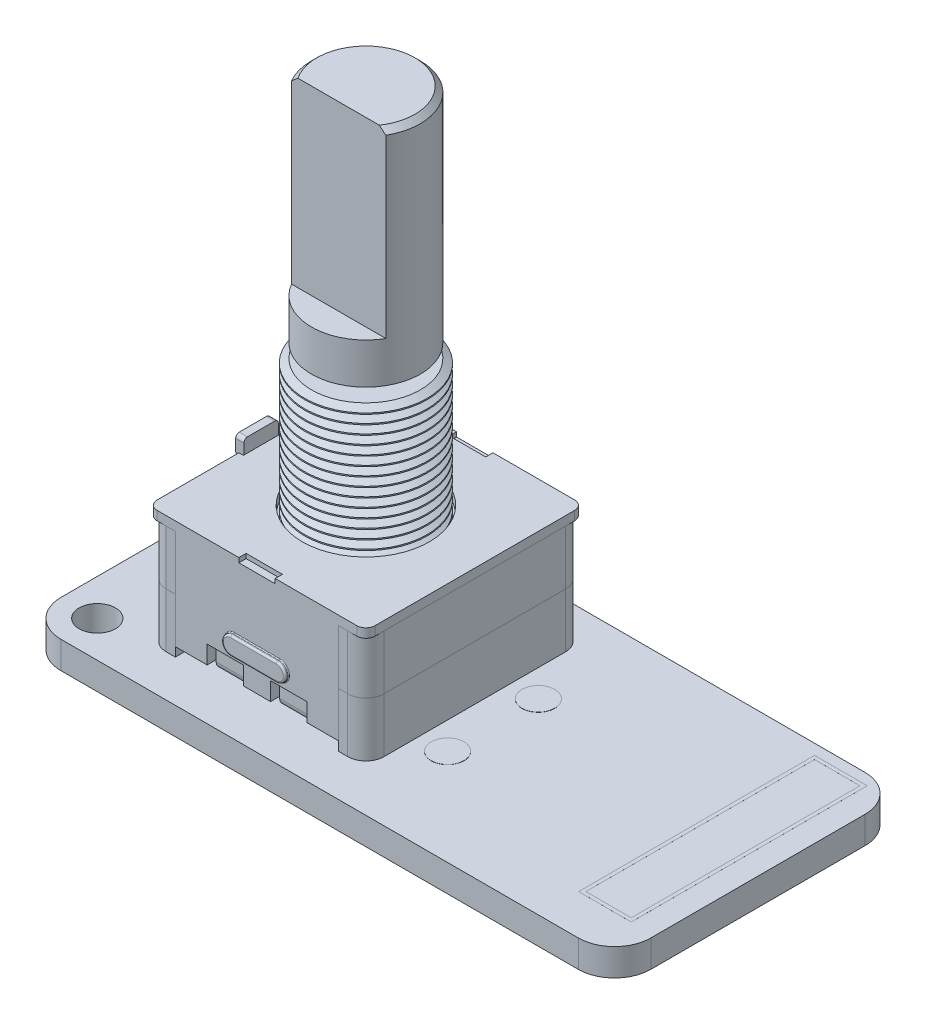
SolidWorks part; units mm, degrees
other "Knob Stem"
material "6061-T6 (SS)"
ref_plane "Front Plane" through (0, 0, 0) normal (0, 0, 1) x (1, 0, 0)
ref_plane "Top Plane" through (0, 0, 0) normal (0, 1, 0) x (1, 0, 0)
ref_plane "Right Plane" through (0, 0, 0) normal (1, 0, 0) x (0, 0, -1)
sketch "Sketch1" plane through (0, 0, 0) normal (0, 1, 0) x (1, 0, 0)
  line L1 (-11, 8) -> (21.5, 8)
  line L2 (-11, 8) -> (-11, -7.8)
  line L3 (-11, -7.8) -> (21.5, -7.8)
  line L4 (21.5, 8) -> (21.5, -7.8)
  dimension "D1" = 32.5
  dimension "D2" = 15.8
  dimension "D3" = 8
  dimension "D4" = 11
extrude "Boss-Extrude1" add sketch "Sketch1" against normal blind 1.5
sketch "Sketch3" plane through (0, -1.5, 0) normal (0, -1, 0) x (1, 0, 0)
  line L0 (-3.75, -1) -> (3.75, -1) construction
  line L1 (-0.5, 0.625) -> (0.5, 0.625)
  line L2 (-0.5, 0.625) -> (-0.5, -2.625)
  line L3 (-0.5, -2.625) -> (0.5, -2.625)
  line L4 (0.5, 0.625) -> (0.5, -2.625)
  line L5 (-0.5, 0.625) -> (0.5, -2.625) construction
  line L6 (-0.5, -2.625) -> (0.5, 0.625) construction
  line L7 (0, -1) -> (0, 0) construction
  line L8 (3.25, 0.625) -> (4.25, 0.625)
  line L9 (3.25, 0.625) -> (3.25, -2.625)
  line L10 (3.25, -2.625) -> (4.25, -2.625)
  line L11 (4.25, 0.625) -> (4.25, -2.625)
  line L12 (3.25, 0.625) -> (4.25, -2.625) construction
  line L13 (3.25, -2.625) -> (4.25, 0.625) construction
  line L14 (-3.25, 0.625) -> (-4.25, 0.625)
  line L15 (-3.25, 0.625) -> (-3.25, -2.625)
  line L16 (-3.25, -2.625) -> (-4.25, -2.625)
  line L17 (-4.25, 0.625) -> (-4.25, -2.625)
  line L18 (-3.25, 0.625) -> (-4.25, -2.625) construction
  line L19 (-3.25, -2.625) -> (-4.25, 0.625) construction
  line L20 (21.5, -8) -> (-11, -8) construction
  point P0 (0, -1)
  dimension "D1" = 3.25
  dimension "D2" = 1
  dimension "D3" = 8.5
  dimension "D4" = 7
extrude "Boss-Extrude2" add sketch "Sketch3" along normal blind 0.001
sketch "Sketch4" plane through (0, -1.501, 0) normal (0, -1, 0) x (1, 0, 0)
  line L0 (-0.5, -1) -> (0.5, -1) construction
  line L2 (3.25, -1) -> (4.25, -1) construction
  line L3 (3.25, 0.625) -> (3.25, -2.625) construction
  line L4 (4.25, -2.625) -> (4.25, 0.625) construction
  line L5 (-3.25, -1) -> (-4.25, -1) construction
  line L6 (-3.25, -2.625) -> (-3.25, 0.625) construction
  line L7 (-4.25, 0.625) -> (-4.25, -2.625) construction
  line L9 (-0.625, 0.125) -> (0.625, 0.125)
  line L10 (-0.625, 0.125) -> (-0.625, -2.125)
  line L11 (-0.625, -2.125) -> (0.625, -2.125)
  line L12 (0.625, 0.125) -> (0.625, -2.125)
  line L13 (-0.625, 0.125) -> (0.625, -2.125) construction
  line L14 (-0.625, -2.125) -> (0.625, 0.125) construction
  line L15 (3.125, 0.125) -> (4.375, 0.125)
  line L16 (3.125, 0.125) -> (3.125, -2.125)
  line L17 (3.125, -2.125) -> (4.375, -2.125)
  line L18 (4.375, 0.125) -> (4.375, -2.125)
  line L19 (3.125, 0.125) -> (4.375, -2.125) construction
  line L20 (3.125, -2.125) -> (4.375, 0.125) construction
  line L21 (-4.375, 0.125) -> (-3.125, 0.125)
  line L22 (-4.375, 0.125) -> (-4.375, -2.125)
  line L23 (-4.375, -2.125) -> (-3.125, -2.125)
  line L24 (-3.125, 0.125) -> (-3.125, -2.125)
  line L25 (-4.375, 0.125) -> (-3.125, -2.125) construction
  line L26 (-4.375, -2.125) -> (-3.125, 0.125) construction
  line L27 (-0.5, 0.625) -> (-0.5, -2.625) construction
  line L28 (0.5, -2.625) -> (0.5, 0.625) construction
  point P17 (0, -1)
  point P22 (3.75, -1)
  point P27 (-3.75, -1)
  dimension "D1" = 1.25
  dimension "D2" = 2.25
extrude "Boss-Extrude3" add sketch "Sketch4" along normal blind 0.3
sketch "Sketch5" plane through (0, -1.801, 0) normal (0, -1, 0) x (1, 0, 0)
  line L0 (-0.625, 0.125) -> (-0.625, -2.125) construction
  line L2 (-0.625, -1) -> (-3.125, -1) construction
  line L3 (-3.125, -1) -> (-4.375, -1) construction
  line L4 (-4.375, 0.125) -> (-4.375, -2.125) construction
  line L5 (-3.125, -2.125) -> (-3.125, 0.125) construction
  line L6 (0.625, -1) -> (3.125, -1) construction
  line L7 (3.125, 0.125) -> (3.125, -2.125) construction
  line L8 (3.125, -1) -> (4.375, -1) construction
  line L9 (4.375, -2.125) -> (4.375, 0.125) construction
  line L10 (0.625, -2.125) -> (0.625, 0.125) construction
  line L15 (-0.625, -1) -> (0.625, -1) construction
  line L17 (-0.625, -0.1) -> (0.625, -0.1)
  line L18 (-4.375, -0.1) -> (-3.125, -0.1)
  line L19 (-4.375, -0.1) -> (-4.375, -1.9)
  line L20 (-4.375, -1.9) -> (-3.125, -1.9)
  line L21 (-3.125, -0.1) -> (-3.125, -1.9)
  line L22 (-4.375, -0.1) -> (-3.125, -1.9) construction
  line L23 (-4.375, -1.9) -> (-3.125, -0.1) construction
  line L24 (3.125, -0.1) -> (4.375, -0.1)
  line L25 (3.125, -0.1) -> (3.125, -1.9)
  line L26 (3.125, -1.9) -> (4.375, -1.9)
  line L27 (4.375, -0.1) -> (4.375, -1.9)
  line L28 (3.125, -0.1) -> (4.375, -1.9) construction
  line L29 (3.125, -1.9) -> (4.375, -0.1) construction
  line L30 (-0.625, -0.1) -> (-0.625, -1.9)
  line L31 (-0.625, -1.9) -> (0.625, -1.9)
  line L32 (0.625, -0.1) -> (0.625, -1.9)
  line L33 (-0.625, -0.1) -> (0.625, -1.9) construction
  line L34 (-0.625, -1.9) -> (0.625, -0.1) construction
  point P4 (0, -1)
  point P24 (-3.75, -1)
  point P29 (3.75, -1)
  dimension "D1" = 1.8
extrude "Boss-Extrude4" add sketch "Sketch5" along normal blind 0.1
sketch "Sketch6" plane through (0, -1.5, 0) normal (0, -1, 0) x (1, 0, 0)
  line L0 (18.75, -8) -> (18.75, -6) construction
  line L1 (-7, 2.5) -> (7, 2.5) construction
  line L2 (-7, 2.5) -> (-7, -2.5) construction
  line L3 (-7, -2.5) -> (7, -2.5) construction
  line L4 (7, 2.5) -> (7, -2.5) construction
  line L5 (-7, 2.5) -> (7, -2.5) construction
  line L6 (-7, -2.5) -> (7, 2.5) construction
  line L7 (21.5, -8) -> (-11, -8) construction
  line L8 (18.75, -6) -> (18.75, -3.46) construction
  line L9 (18.75, -3.46) -> (18.75, -0.92) construction
  line L10 (18.75, -0.92) -> (18.75, 1.62) construction
  line L11 (18.75, 1.62) -> (18.75, 4.16) construction
  line L12 (21.5, 7.8) -> (21.5, -8) construction
  circle A0 centre (7, 2.5) radius 0.6
  circle A1 centre (7, -2.5) radius 0.6
  circle A2 centre (-7, -2.5) radius 0.6
  circle A3 centre (-7, 2.5) radius 0.6
  circle A4 centre (-7, 0) radius 0.6
  circle A5 centre (18.75, 4.16) radius 0.6
  circle A6 centre (18.75, 1.62) radius 0.6
  circle A7 centre (18.75, -0.92) radius 0.6
  circle A8 centre (18.75, -3.46) radius 0.6
  circle A9 centre (18.75, -6) radius 0.6
  point P0 (0, 0)
  dimension "D3" = 1.2
  dimension "D4" = 2.54
  dimension "D1" = 5
  dimension "D2" = 14
  dimension "D5" = 2
  dimension "D6" = 2.75
extrude "Boss-Extrude5" add sketch "Sketch6" along normal blind 0.01
sketch "Sketch7" plane through (0, -1.5, 0) normal (0, -1, 0) x (1, 0, 0)
  line L1 (-7.325, -2.175) -> (-6.675, -2.175)
  line L2 (-7.325, -2.175) -> (-7.325, -2.825)
  line L3 (-7.325, -2.825) -> (-6.675, -2.825)
  line L4 (-6.675, -2.175) -> (-6.675, -2.825)
  line L5 (-7.325, -2.175) -> (-6.675, -2.825) construction
  line L6 (-7.325, -2.825) -> (-6.675, -2.175) construction
  line L7 (-7.325, 0.325) -> (-6.675, 0.325)
  line L8 (-7.325, 0.325) -> (-7.325, -0.325)
  line L9 (-7.325, -0.325) -> (-6.675, -0.325)
  line L10 (-6.675, 0.325) -> (-6.675, -0.325)
  line L11 (-7.325, 0.325) -> (-6.675, -0.325) construction
  line L12 (-7.325, -0.325) -> (-6.675, 0.325) construction
  line L13 (-7.325, 2.825) -> (-6.675, 2.825)
  line L14 (-7.325, 2.825) -> (-7.325, 2.175)
  line L15 (-7.325, 2.175) -> (-6.675, 2.175)
  line L16 (-6.675, 2.825) -> (-6.675, 2.175)
  line L17 (-7.325, 2.825) -> (-6.675, 2.175) construction
  line L18 (-7.325, 2.175) -> (-6.675, 2.825) construction
  line L19 (6.675, -2.175) -> (7.325, -2.175)
  line L20 (6.675, -2.175) -> (6.675, -2.825)
  line L21 (6.675, -2.825) -> (7.325, -2.825)
  line L22 (7.325, -2.175) -> (7.325, -2.825)
  line L23 (6.675, -2.175) -> (7.325, -2.825) construction
  line L24 (6.675, -2.825) -> (7.325, -2.175) construction
  line L25 (6.675, 2.825) -> (7.325, 2.825)
  line L26 (6.675, 2.825) -> (6.675, 2.175)
  line L27 (6.675, 2.175) -> (7.325, 2.175)
  line L28 (7.325, 2.825) -> (7.325, 2.175)
  line L29 (6.675, 2.825) -> (7.325, 2.175) construction
  line L30 (6.675, 2.175) -> (7.325, 2.825) construction
  line L31 (18.425, 4.485) -> (19.075, 4.485)
  line L32 (18.425, 4.485) -> (18.425, 3.835)
  line L33 (18.425, 3.835) -> (19.075, 3.835)
  line L34 (19.075, 4.485) -> (19.075, 3.835)
  line L35 (18.425, 4.485) -> (19.075, 3.835) construction
  line L36 (18.425, 3.835) -> (19.075, 4.485) construction
  line L37 (18.425, 1.945) -> (19.075, 1.945)
  line L38 (18.425, 1.945) -> (18.425, 1.295)
  line L39 (18.425, 1.295) -> (19.075, 1.295)
  line L40 (19.075, 1.945) -> (19.075, 1.295)
  line L41 (18.425, 1.945) -> (19.075, 1.295) construction
  line L42 (18.425, 1.295) -> (19.075, 1.945) construction
  line L43 (18.425, -0.595) -> (19.075, -0.595)
  line L44 (18.425, -0.595) -> (18.425, -1.245)
  line L45 (18.425, -1.245) -> (19.075, -1.245)
  line L46 (19.075, -0.595) -> (19.075, -1.245)
  line L47 (18.425, -0.595) -> (19.075, -1.245) construction
  line L48 (18.425, -1.245) -> (19.075, -0.595) construction
  line L49 (18.425, -3.135) -> (19.075, -3.135)
  line L50 (18.425, -3.135) -> (18.425, -3.785)
  line L51 (18.425, -3.785) -> (19.075, -3.785)
  line L52 (19.075, -3.135) -> (19.075, -3.785)
  line L53 (18.425, -3.135) -> (19.075, -3.785) construction
  line L54 (18.425, -3.785) -> (19.075, -3.135) construction
  line L55 (18.425, -5.675) -> (19.075, -5.675)
  line L56 (18.425, -5.675) -> (18.425, -6.325)
  line L57 (18.425, -6.325) -> (19.075, -6.325)
  line L58 (19.075, -5.675) -> (19.075, -6.325)
  line L59 (18.425, -5.675) -> (19.075, -6.325) construction
  line L60 (18.425, -6.325) -> (19.075, -5.675) construction
  point P0 (-7, -2.5)
  point P5 (-7, 0)
  point P11 (-7, 2.5)
  point P17 (7, -2.5)
  point P23 (7, 2.5)
  point P29 (18.75, 4.16)
  point P35 (18.75, 1.62)
  point P41 (18.75, -0.92)
  point P47 (18.75, -3.46)
  point P53 (18.75, -6)
  dimension "D1" = 0.65
sketch "Sketch9" plane through (0, -1.5, 0) normal (0, -1, 0) x (1, 0, 0)
  line L0 (3.25, 0.625) -> (4.25, -2.625) construction
  line L1 (-0.8, 0.75) -> (0.8, 0.75)
  line L2 (-0.8, 0.75) -> (-0.8, -0.875)
  line L3 (-0.8, -2.75) -> (0.8, -2.75)
  line L4 (0.8, 0.75) -> (0.8, -0.875)
  line L5 (-0.8, 0.75) -> (0.8, -2.75) construction
  line L6 (-0.8, -2.75) -> (0.8, 0.75) construction
  line L7 (2.95, 0.75) -> (4.55, 0.75)
  line L8 (2.95, 0.75) -> (2.95, -0.875)
  line L9 (2.95, -2.75) -> (4.55, -2.75)
  line L10 (4.55, 0.75) -> (4.55, -0.875)
  line L11 (2.95, 0.75) -> (4.55, -2.75) construction
  line L12 (2.95, -2.75) -> (4.55, 0.75) construction
  line L13 (-4.75, -2.95) -> (-2.75, -2.95)
  line L14 (-4.55, 0.75) -> (-2.95, 0.75)
  line L15 (-4.55, 0.75) -> (-4.55, -0.875)
  line L16 (-4.55, -2.75) -> (-2.95, -2.75)
  line L17 (-2.95, 0.75) -> (-2.95, -0.875)
  line L18 (-4.55, 0.75) -> (-2.95, -2.75) construction
  line L19 (-4.55, -2.75) -> (-2.95, 0.75) construction
  line L20 (-2.75, 0.95) -> (-2.75, -0.875)
  line L21 (-4.75, 0.95) -> (-2.75, 0.95)
  line L22 (-4.75, 0.95) -> (-4.75, -0.875)
  line L23 (-1, 0.95) -> (-1, -0.875)
  line L24 (-1, -2.95) -> (1, -2.95)
  line L25 (1, 0.95) -> (1, -0.875)
  line L26 (-1, 0.95) -> (1, 0.95)
  line L27 (2.75, -2.95) -> (4.75, -2.95)
  line L28 (4.75, 0.95) -> (4.75, -0.875)
  line L29 (2.75, 0.95) -> (4.75, 0.95)
  line L30 (2.75, 0.95) -> (2.75, -0.875)
  line L31 (0, -0.875) -> (0, -1.125) construction
  line L32 (0, -0.875) -> (-0.8, -0.875) construction
  line L33 (0, -1.125) -> (-0.8, -1.125) construction
  line L34 (0, -0.875) -> (0.8, -0.875) construction
  line L35 (0, -1.125) -> (0.8, -1.125) construction
  line L36 (-0.8, -0.875) -> (-1, -0.875)
  line L37 (-0.8, -1.125) -> (-1, -1.125)
  line L38 (0.8, -0.875) -> (1, -0.875)
  line L39 (0.8, -1.125) -> (1, -1.125)
  line L40 (-0.8, -1.125) -> (-0.8, -2.75)
  line L41 (-0.8, 0.75) -> (-0.8, -2.75) construction
  line L42 (-1, -1.125) -> (-1, -2.95)
  line L43 (-1, 0.95) -> (-1, -2.95) construction
  line L44 (1, -1.125) -> (1, -2.95)
  line L45 (1, 0.95) -> (1, -2.95) construction
  line L46 (0.8, -1.125) -> (0.8, -2.75)
  line L47 (0.8, 0.75) -> (0.8, -2.75) construction
  line L48 (-2.95, 0.75) -> (-0.8, 0.75) construction
  line L49 (1, -0.875) -> (2.75, -0.875) construction
  line L50 (1, -1.125) -> (2.75, -1.125) construction
  line L51 (-1, -0.875) -> (-2.75, -0.875) construction
  line L52 (-1, -1.125) -> (-2.75, -1.125) construction
  line L53 (-2.75, -0.875) -> (-2.95, -0.875)
  line L54 (-2.75, -1.125) -> (-2.95, -1.125)
  line L55 (2.75, -0.875) -> (2.95, -0.875)
  line L56 (2.75, -1.125) -> (2.95, -1.125)
  line L57 (2.95, -0.875) -> (4.55, -0.875) construction
  line L58 (2.95, -1.125) -> (4.55, -1.125) construction
  line L59 (4.55, -0.875) -> (4.75, -0.875)
  line L60 (4.55, -1.125) -> (4.75, -1.125)
  line L61 (2.95, -1.125) -> (2.95, -2.75)
  line L62 (2.95, 0.75) -> (2.95, -2.75) construction
  line L63 (2.75, -1.125) -> (2.75, -2.95)
  line L64 (2.75, 0.95) -> (2.75, -2.95) construction
  line L65 (4.75, -1.125) -> (4.75, -2.95)
  line L66 (4.75, 0.95) -> (4.75, -2.95) construction
  line L67 (4.55, -1.125) -> (4.55, -2.75)
  line L68 (4.55, 0.75) -> (4.55, -2.75) construction
  line L69 (0.8, 0.75) -> (2.95, 0.75) construction
  line L70 (-2.95, -0.875) -> (-4.55, -0.875) construction
  line L71 (-2.95, -1.125) -> (-4.55, -1.125) construction
  line L72 (-4.55, -0.875) -> (-4.75, -0.875)
  line L73 (-4.55, -1.125) -> (-4.75, -1.125)
  line L74 (-4.55, -1.125) -> (-4.55, -2.75)
  line L75 (-4.55, 0.75) -> (-4.55, -2.75) construction
  line L76 (-4.75, -1.125) -> (-4.75, -2.95)
  line L77 (-4.75, 0.95) -> (-4.75, -2.95) construction
  line L78 (-2.75, -1.125) -> (-2.75, -2.95)
  line L79 (-2.75, 0.95) -> (-2.75, -2.95) construction
  line L80 (-2.95, -1.125) -> (-2.95, -2.75)
  line L81 (-2.95, 0.75) -> (-2.95, -2.75) construction
  point P0 (0, -1)
  point P5 (3.75, -1)
  point P13 (-3.75, -1)
  dimension "D1" = 3.5
  dimension "D2" = 1.6
  dimension "D6" = 0.25
  dimension "D3" = 0.2
  dimension "D4" = 0.2
  dimension "D5" = 0.2
extrude "Boss-Extrude7" add sketch "Sketch9" along normal blind 0.001
sketch "Sketch10" plane through (0, -1.5, 0) normal (0, -1, 0) x (1, 0, 0)
  line L0 (-3.75, -2.95) -> (-3.75, -3.25) construction
  line L1 (-4.75, -2.95) -> (-2.75, -2.95) construction
  line L2 (0, -2.95) -> (0, -3.25) construction
  line L3 (-1, -2.95) -> (1, -2.95) construction
  line L4 (3.75, -2.95) -> (3.75, -3.25) construction
  line L5 (2.75, -2.95) -> (4.75, -2.95) construction
  line L6 (-1.25, -3.25) -> (1.25, -3.25) construction
  line L7 (-5, -3.25) -> (-2.5, -3.25) construction
  line L8 (2.5, -3.25) -> (5, -3.25) construction
  line L9 (21.5, -8) -> (-11, -8) construction
  text T0 "R1" font "Calibri" height 0.75
  text T1 "R2" font "Calibri" height 0.75
  text T2 "R3" font "Calibri" height 0.75
  dimension "D1" = 2.5
  dimension "D2" = 4.75
extrude "Boss-Extrude8" add sketch "Sketch10" along normal blind 0.001
sketch "Sketch12" plane through (0, 0, 0) normal (0, 1, 0) x (1, 0, 0)
  line L0 (17.3, 7.42) -> (20.2, 7.42)
  line L1 (17.5, -5.38) -> (20, -5.38)
  line L2 (17.5, -5.38) -> (17.5, 7.22)
  line L3 (17.5, 7.22) -> (20, 7.22)
  line L4 (20, -5.38) -> (20, 7.22)
  line L5 (17.5, -5.38) -> (20, 7.22) construction
  line L6 (17.5, 7.22) -> (20, -5.38) construction
  line L7 (20.2, -5.58) -> (20.2, 7.42)
  line L8 (17.3, -5.58) -> (20.2, -5.58)
  line L9 (17.3, -5.58) -> (17.3, 7.42)
  point P0 (18.75, 0.92)
  dimension "D1" = 12.6
  dimension "D2" = 2.5
  dimension "D3" = 0.2
extrude "Boss-Extrude10" add sketch "Sketch12" along normal blind 0.001
sketch "Sketch13" plane through (0, 0, 0) normal (0, 1, 0) x (1, 0, 0)
  circle A0 centre (-7, -2.5) radius 0.6 construction
  circle A1 centre (-7, -2.5) radius 0.6 construction
  circle A2 centre (-7, 0) radius 0.6 construction
  circle A3 centre (-7, 0) radius 0.6 construction
  circle A4 centre (-7, 2.5) radius 0.6 construction
  circle A5 centre (-7, 2.5) radius 0.6 construction
  circle A6 centre (7, -2.5) radius 0.6 construction
  circle A7 centre (7, -2.5) radius 0.6 construction
  circle A8 centre (7, 2.5) radius 0.6 construction
  circle A9 centre (7, 2.5) radius 0.6 construction
  circle A10 centre (-7, -2.5) radius 0.9
  circle A11 centre (-7, 0) radius 0.9
  circle A12 centre (-7, 2.5) radius 0.9
  circle A13 centre (7, 2.5) radius 0.9
  circle A14 centre (7, -2.5) radius 0.9
  dimension "D1" = 1.8
extrude "Boss-Extrude11" add sketch "Sketch13" along normal blind 0.01
ref_plane "Plane3" through (0, 6.5, 0) normal (0, 1, 0) x (1, 0, 0)
sketch "Sketch27" plane through (0, 6.5, 0) normal (0, 1, 0) x (1, 0, 0)
  line L0 (-6, 0) -> (6, 0) construction
  line L5 (-6, 5) -> (-6, -5)
  line L6 (6, 5) -> (6, -5)
  line L7 (0, 5.5) -> (0, -5.5) construction
  line L8 (-4.5, 5.5) -> (4.5, 5.5)
  line L9 (-4.5, -5.5) -> (4.5, -5.5)
  line L10 (-4.5, 5.5) -> (-4.5, 6)
  line L11 (-4.5, 6) -> (-5, 6)
  line L12 (4.5, 5.5) -> (4.5, 6)
  line L13 (4.5, 6) -> (5, 6)
  line L14 (-4.5, -5.5) -> (-4.5, -6)
  line L15 (-4.5, -6) -> (-5, -6)
  line L16 (4.5, -5.5) -> (4.5, -6)
  line L17 (4.5, -6) -> (5, -6)
  arc A0 (-6, 5) -> (-5, 6) centre (-5, 5) cw
  arc A1 (-6, -5) -> (-5, -6) centre (-5, -5) ccw
  arc A2 (6, -5) -> (5, -6) centre (5, -5) cw
  arc A3 (6, 5) -> (5, 6) centre (5, 5) ccw
  dimension "D5" = 1
  dimension "D1" = 0.5
  dimension "D2" = 12
  dimension "D3" = 9
  dimension "D4" = 12
extrude "Boss-Extrude18" add sketch "Sketch27" against normal blind 3 separate body
sketch "Sketch55" plane through (0, 3.5, 0) normal (0, -1, 0) x (1, 0, 0)
  circle A0 centre (0, 0) radius 4.3192
extrude "Cut-Extrude14" cut sketch "Sketch55" against normal blind 2.2
sketch "Sketch28" plane through (0, 3.5, 0) normal (0, -1, 0) x (1, 0, 0)
  line L12 (-5, -6) -> (-4.5, -6)
  line L13 (-4.5, -6) -> (-4.5, -5.5)
  line L14 (-4.5, -5.5) -> (4.5, -5.5)
  line L15 (4.5, -5.5) -> (4.5, -6)
  line L16 (4.5, -6) -> (5, -6)
  line L17 (6, -5) -> (6, 5)
  line L18 (5, 6) -> (4.5, 6)
  line L19 (4.5, 6) -> (4.5, 5.5)
  line L20 (4.5, 5.5) -> (-4.5, 5.5)
  line L21 (-4.5, 5.5) -> (-4.5, 6)
  line L22 (-4.5, 6) -> (-5, 6)
  line L23 (-6, 5) -> (-6, -5)
  line L24 (-5, -6) -> (-4.5, -6)
  line L25 (-4.5, -6) -> (-4.5, -5.5)
  line L26 (-4.5, -5.5) -> (4.5, -5.5)
  line L27 (4.5, -5.5) -> (4.5, -6)
  line L28 (4.5, -6) -> (5, -6)
  line L29 (6, -5) -> (6, 5)
  line L30 (5, 6) -> (4.5, 6)
  line L31 (4.5, 6) -> (4.5, 5.5)
  line L32 (4.5, 5.5) -> (-4.5, 5.5)
  line L33 (-4.5, 5.5) -> (-4.5, 6)
  line L34 (-4.5, 6) -> (-5, 6)
  line L35 (-6, 5) -> (-6, -5)
  arc A4 (-6, -5) -> (-5, -6) centre (-5, -5) ccw
  arc A5 (5, -6) -> (6, -5) centre (5, -5) ccw
  arc A6 (6, 5) -> (5, 6) centre (5, 5) ccw
  arc A7 (-5, 6) -> (-6, 5) centre (-5, 5) ccw
  arc A8 (-6, -5) -> (-5, -6) centre (-5, -5) ccw
  arc A9 (5, -6) -> (6, -5) centre (5, -5) ccw
  arc A10 (6, 5) -> (5, 6) centre (5, 5) ccw
  arc A11 (-5, 6) -> (-6, 5) centre (-5, 5) ccw
  dimension "D1" = 0
extrude "Boss-Extrude19" add sketch "Sketch28" along normal blind 3 separate body
sketch "Sketch29" plane through (0, 6.5, 0) normal (0, 1, 0) x (1, 0, 0)
  line L0 (-6, 0) -> (6, 0) construction
  line L1 (-5.5, 6) -> (5.5, 6)
  line L2 (-6, 5.5) -> (-6, -5.5)
  line L3 (-5.5, -6) -> (5.5, -6)
  line L4 (6, 5.5) -> (6, -5.5)
  arc A0 (-5.5, 6) -> (-6, 5.5) centre (-5.5, 5.5) ccw
  arc A1 (-6, -5.5) -> (-5.5, -6) centre (-5.5, -5.5) ccw
  arc A2 (5.5, -6) -> (6, -5.5) centre (5.5, -5.5) ccw
  arc A3 (5.5, 6) -> (6, 5.5) centre (5.5, 5.5) cw
  dimension "D3" = 0.5
  dimension "D1" = 12
  dimension "D2" = 12
extrude "Boss-Extrude20" add sketch "Sketch29" along normal blind 0.5 separate body
sketch "Sketch30" plane through (0, 6.5, 0) normal (0, -1, 0) x (1, 0, 0)
  line L0 (-4.5, 5.5) -> (4.5, 5.5) construction
  line L1 (-4.5, 5.5) -> (4.5, 5.5)
  line L2 (-4.5, 6) -> (-4.5, 5.5) construction
  line L3 (-4.5, 6) -> (-4.5, 5.5)
  line L4 (4.5, 5.5) -> (4.5, 6) construction
  line L5 (4.5, 5.5) -> (4.5, 6)
  line L6 (-4.5, 6) -> (4.5, 6)
  line L7 (-4.5, -5.5) -> (-4.5, -6) construction
  line L8 (4.5, -6) -> (4.5, -5.5) construction
  line L9 (4.5, -5.5) -> (-4.5, -5.5) construction
  line L10 (-4.5, -5.5) -> (-4.5, -6)
  line L11 (4.5, -6) -> (4.5, -5.5)
  line L12 (4.5, -5.5) -> (-4.5, -5.5)
  line L13 (-4.5, -6) -> (4.5, -6)
extrude "Boss-Extrude21" add sketch "Sketch30" along normal blind 5.5
sketch "Sketch31" plane through (0, 0, -6) normal (0, 0, -1) x (-1, 0, 0)
  line L0 (0, 0) -> (0, 1) construction
  line L1 (4.5, 1) -> (-4.5, 1) construction
  line L2 (-0.75, 1) -> (0.75, 1) construction
  line L4 (0.75, 1) -> (2.75, 1)
  line L5 (0.75, 1) -> (0.75, 2)
  line L6 (0.75, 2) -> (2.75, 2)
  line L7 (2.75, 1) -> (2.75, 2)
  line L8 (-0.75, 1) -> (-2.75, 1)
  line L9 (-0.75, 1) -> (-0.75, 2)
  line L10 (-0.75, 2) -> (-2.75, 2)
  line L11 (-2.75, 1) -> (-2.75, 2)
  dimension "D1" = 1.5
  dimension "D2" = 2
  dimension "D3" = 1
extrude "Cut-Extrude2" cut sketch "Sketch31" against normal up to surface (12 mm away) up to face at (0, 5.25, 6)
sketch "Sketch32" plane through (0, 0, 6) normal (0, 0, 1) x (1, 0, 0)
  line L0 (0, 0) -> (0, 1) construction
  line L1 (0.75, 1) -> (-0.75, 1) construction
  line L2 (0, 1) -> (0, 2.75) construction
  line L3 (-1.25, 2.75) -> (1.25, 2.75) construction
  line L4 (-1.25, 3.25) -> (1.25, 3.25)
  line L5 (-1.25, 2.25) -> (1.25, 2.25)
  line L6 (1.25, 2.75) -> (1.75, 2.75) construction
  line L7 (-1.25, 2.75) -> (-1.75, 2.75) construction
  arc A0 (-1.25, 3.25) -> (-1.25, 2.25) centre (-1.25, 2.75) ccw
  arc A1 (1.25, 2.25) -> (1.25, 3.25) centre (1.25, 2.75) ccw
  point P8 (0, 2.75)
  dimension "D1" = 1
  dimension "D2" = 3.5
  dimension "D3" = 1.75
extrude "Boss-Extrude22" add sketch "Sketch32" along normal blind 0.2
sketch "Sketch33" plane through (0, 0, -6) normal (0, 0, -1) x (-1, 0, 0)
  line L2 (1.25, 3.25) -> (-1.25, 3.25)
  line L3 (-1.25, 2.25) -> (1.25, 2.25)
  line L4 (1.25, 3.25) -> (-1.25, 3.25)
  line L5 (-1.25, 2.25) -> (1.25, 2.25)
  arc A2 (-1.25, 3.25) -> (-1.25, 2.25) centre (-1.25, 2.75) ccw
  arc A3 (1.25, 2.25) -> (1.25, 3.25) centre (1.25, 2.75) ccw
  arc A4 (-1.25, 3.25) -> (-1.25, 2.25) centre (-1.25, 2.75) ccw
  arc A5 (1.25, 2.25) -> (1.25, 3.25) centre (1.25, 2.75) ccw
  dimension "D1" = 0
extrude "Boss-Extrude23" add sketch "Sketch33" along normal blind 0.2
fillet "Fillet4" radius 0.1 8 edges at (0, 2.25, -6.2) (1.75, 2.75, -6.2) (0, 3.25, -6.2) (-1.75, 2.75, -6.2) (0, 3.25, 6.2) (1.75, 2.75, 6.2) (0, 2.25, 6.2) (-1.75, 2.75, 6.2)
fillet "Fillet5" radius 0.05 8 edges at (-1.75, 2.75, -6) (0, 2.25, -6) (1.75, 2.75, -6) (1.75, 2.75, 6) (0, 2.25, 6) (-1.75, 2.75, 6) (0, 3.25, -6) (0, 3.25, 6)
sketch "Sketch34" plane through (0, 7, 0) normal (0, 1, 0) x (1, 0, 0)
  line L0 (0, 0) -> (-6, 0) construction
  line L1 (-6, 5.5) -> (-6, -5.5) construction
  line L2 (0, 5.6) -> (0, -5.6) construction
  line L3 (-6, 1) -> (-6.5, 1)
  line L4 (-6, 1) -> (-6, -1) construction
  line L5 (-6, -1) -> (-6.5, -1)
  line L6 (-6.5, 1) -> (-6.5, -1)
  line L7 (0, 5.6) -> (0, 6) construction
  line L8 (-1, 6) -> (1, 6)
  line L9 (-1, 6) -> (-1, 5.6)
  line L10 (-1, 5.6) -> (1, 5.6)
  line L11 (1, 6) -> (1, 5.6)
  line L12 (1.25, 6) -> (-1.25, 6) construction
  line L13 (-5.5, -6) -> (5.5, -6) construction
  line L14 (-1, -5.6) -> (1, -5.6)
  line L15 (-1, -5.6) -> (-1, -6)
  line L16 (-1, -6) -> (1, -6)
  line L17 (1, -5.6) -> (1, -6)
  line L18 (-6, 1) -> (-5.75, 1)
  line L19 (-5.75, 1) -> (-5.75, -1)
  line L20 (-5.75, -1) -> (-6, -1)
  dimension "D1" = 2
  dimension "D2" = 0.5
  dimension "D3" = 0.4
  dimension "D4" = 2
  dimension "D5" = 0.75
extrude "Cut-Extrude3" cut sketch "Sketch34" against normal blind 0.25
sketch "Sketch35" plane through (0, 6.75, 0) normal (0, 1, 0) x (1, 0, 0)
  line L0 (-6, -1) -> (-6, 1) construction
  line L1 (-6.225, 0.95) -> (-5.775, 0.95)
  line L2 (-6.225, 0.95) -> (-6.225, -0.95)
  line L3 (-6.225, -0.95) -> (-5.775, -0.95)
  line L4 (-5.775, 0.95) -> (-5.775, -0.95)
  line L5 (-6.225, 0.95) -> (-5.775, -0.95) construction
  line L6 (-6.225, -0.95) -> (-5.775, 0.95) construction
  point P0 (-6, 0)
  dimension "D1" = 0.45
  dimension "D2" = 1.9
extrude "Boss-Extrude24" add sketch "Sketch35" along normal blind 1
fillet "Fillet6" radius 0.2 2 edges at (-6, 7.75, -0.95) (-6, 7.75, 0.95)
fillet "Fillet7" radius 0.2 1 edges at (-6.225, 6.75, 0)
sketch "Sketch36" plane through (0, 7, 0) normal (0, 1, 0) x (1, 0, 0)
  circle A0 centre (0, 0) radius 3.5
  dimension "D1" = 7
extrude "Cut-Extrude4" cut sketch "Sketch36" against normal up to surface (0.5 mm away) up to face at (0, 6.5, 0)
sketch "Sketch37" plane through (0, 6.5, 0) normal (0, 1, 0) x (1, 0, 0)
  circle A0 centre (0, 0) radius 3.375
  dimension "D1" = 6.75
extrude "Boss-Extrude25" add sketch "Sketch37" along normal blind 7.5
sketch "Sketch38" plane through (0, 14, 0) normal (0, 1, 0) x (1, 0, 0)
  circle A0 centre (0, 0) radius 1.5
  dimension "D1" = 3
extrude "Cut-Extrude5" cut sketch "Sketch38" against normal blind 5
sketch "Sketch39" plane through (0, 0, 0) normal (0, 0, 1) x (1, 0, 0)
  line L0 (0, 0) -> (0, 6.5) construction
  line L1 (0, 6.5) -> (0, 14) construction
  line L2 (-4.5, 6.5) -> (4.5, 6.5) construction
  line L3 (1.5, 14) -> (-1.5, 14) construction
  line L4 (0, 14) -> (3, 14) construction
  line L5 (3, 14) -> (3.433, 14) construction
  line L6 (3.433, 14) -> (3.933, 14) construction
  line L7 (3.433, 14.25) -> (3.433, 13.75) construction
  line L8 (3.933, 14.25) -> (3.933, 13.75)
  line L9 (3.933, 14.25) -> (3.433, 14.25)
  line L10 (3.933, 13.75) -> (3.433, 13.75)
  line L11 (3.433, 13.75) -> (3, 14)
  line L12 (3, 14) -> (3.433, 14.25)
  dimension "D1" = 0.5
  dimension "D2" = 60
  dimension "D3" = 3
revolve "Cut-Revolve1" cut sketch "Sketch39" angle 360 about L1
pattern_linear "LPattern3" count 15 spacing 0.5 along (0, -1, 0) of "Cut-Revolve1"
ref_plane "Plane4" through (0, 9, 0) normal (0, 1, 0) x (1, 0, 0)
sketch "Sketch40" plane through (0, 9, 0) normal (0, 1, 0) x (1, 0, 0)
  circle A0 centre (0, 0) radius 5.75
  circle A1 centre (0, 0) radius 3.5
  dimension "D1" = 7
  dimension "D2" = 11.5
extrude "Boss-Extrude26" add sketch "Sketch40" along normal blind 0.3 separate body
sketch "Sketch41" plane through (0, 9.3, 0) normal (0, 1, 0) x (1, 0, 0)
  line L1 (2.8868, -5) -> (5.7735, 0)
  line L2 (5.7735, 0) -> (2.8868, 5)
  line L3 (2.8868, 5) -> (-2.8868, 5)
  line L4 (-2.8868, 5) -> (-5.7735, 0)
  line L5 (-5.7735, 0) -> (-2.8868, -5)
  line L6 (-2.8868, -5) -> (2.8868, -5)
  circle A0 centre (0, 0) radius 5 construction
  circle A1 centre (0, 0) radius 3.25
  dimension "D1" = 10
  dimension "D2" = 6.5
extrude "Boss-Extrude27" add sketch "Sketch41" along normal blind 2 separate body
sketch "Sketch42" plane through (0, 0, 0) normal (0, 0, 1) x (1, 0, 0)
  line L0 (0, 0) -> (0, 9.3) construction
  line L1 (-2.8868, 9.3) -> (2.8868, 9.3) construction
  line L2 (0, 9.3) -> (0, 11.3) construction
  line L3 (-2.8868, 11.3) -> (2.8868, 11.3) construction
  line L4 (0, 11.3) -> (4.7735, 11.3) construction
  line L5 (2.8868, 11.3) -> (5.7735, 11.3) construction
  line L6 (4.7735, 11.3) -> (4.7735, 9.3) construction
  line L7 (2.8868, 9.3) -> (5.7735, 9.3) construction
  line L8 (4.7735, 9.3) -> (0, 9.3) construction
  line L9 (4.7735, 9.3) -> (5.7735, 9.3)
  line L10 (5.7735, 9.3) -> (5.7735, 9.664)
  line L11 (5.7735, 11.3) -> (5.7735, 9.3) construction
  line L12 (5.7735, 9.664) -> (4.7735, 9.3)
  line L13 (5.7735, 11.3) -> (5.7735, 10.936)
  line L14 (5.7735, 10.936) -> (4.7735, 11.3)
  line L15 (4.7735, 11.3) -> (5.7735, 11.3)
  dimension "D1" = 1
  dimension "D2" = 20
revolve "Cut-Revolve2" cut sketch "Sketch42" angle 360 about L2
sketch "Sketch43" plane through (0, 0, 0) normal (0, 0, 1) x (1, 0, 0)
  line L0 (0, 0) -> (0, 10) construction
  line L1 (0, 10) -> (0, 27)
  line L2 (0, 27) -> (2.7, 27)
  line L4 (2.7, 27) -> (3, 27) construction
  line L5 (3, 27) -> (3, 26.7) construction
  line L6 (2.7, 27) -> (3, 26.7)
  line L7 (3, 26.7) -> (3, 14.75)
  line L8 (3, 14.75) -> (1.5, 14.75)
  line L9 (1.5, 14.75) -> (1.5, 10)
  line L10 (1.5, 10) -> (0, 10)
  dimension "D1" = 10
  dimension "D2" = 17
  dimension "D3" = 0.3
  dimension "D4" = 3
  dimension "D5" = 1.5
  dimension "D6" = 4.75
revolve "Revolve1" add sketch "Sketch43" angle 360 about L1
sketch "Sketch Set Dial Pointer Angle" plane through (0, 27, 0) normal (0, 1, 0) x (1, 0, 0)
  line L0 (0, 0) -> (-2.7, 0) construction
  line L1 (0, 0) -> (0, -1.5) construction
  line L2 (-2.5981, -1.5) -> (2.5981, -1.5)
  line L3 (0, -1.5) -> (0, -3) construction
  circle A0 centre (0, 0) radius 3 construction
  arc A1 (-2.5981, -1.5) -> (2.5981, -1.5) centre (0, 0) ccw
  circle A2 centre (0, 0) radius 3 construction
  circle A3 centre (0, 0) radius 2.7 construction
  dimension "D1" = 1.5
  dimension "D2" = 90
extrude "Set Dial Pointer Angle" cut sketch "Sketch Set Dial Pointer Angle" against normal blind 10
sketch "Sketch49" plane through (0, 0, 5.5) normal (0, 0, 1) x (1, 0, 0)
  line L0 (4.5, 0.5) -> (-4.5, 0.5) construction
  line L1 (-4.5, 1) -> (-2.75, 1)
  line L2 (-4.5, 1) -> (-4.5, 0.5)
  line L3 (-4.5, 0.5) -> (-2.75, 0.5)
  line L4 (-2.75, 1) -> (-2.75, 0.5)
  line L6 (4.5, 0.5) -> (2.75, 0.5)
  line L7 (4.5, 0.5) -> (4.5, 1)
  line L8 (4.5, 1) -> (2.75, 1)
  line L9 (2.75, 0.5) -> (2.75, 1)
  line L10 (-0.75, 1) -> (0.75, 1)
  line L11 (-0.75, 1) -> (-0.75, 0.5)
  line L12 (-0.75, 0.5) -> (0.75, 0.5)
  line L13 (0.75, 1) -> (0.75, 0.5)
extrude "Cut-Extrude10" cut sketch "Sketch49" against normal up to surface (11 mm away) up to face at (0, 2, -5.5)
fillet "Fillet9" radius 0.4 4 edges at (-1.75, 0.5, -5.5) (1.75, 0.5, -5.5) (-1.75, 0.5, 5.5) (1.75, 0.5, 5.5)
sketch "Sketch50" plane through (0, 17, 0) normal (0, 1, 0) x (1, 0, 0)
  line L0 (2.5981, -1.5) -> (-2.5981, -1.5) construction
  line L1 (2.5981, -1.5) -> (-2.5981, -1.5)
  line L2 (0, 0) -> (0, -1.5) construction
  line L3 (0, 0) -> (0, 2.25) construction
  line L4 (-0.25, 2.25) -> (0.25, 2.25) construction
  line L5 (0, 2.25) -> (0, 7.25) construction
  line L6 (-0.25, 7.25) -> (0.25, 7.25) construction
  line L7 (-0.25, 7.25) -> (-0.25, 2.25) construction
  line L8 (0.25, 7.25) -> (0.25, 2.25) construction
  circle A0 centre (0, 0) radius 3 construction
  arc A1 (2.5981, -1.5) -> (-2.5981, -1.5) centre (0, 0) ccw
  circle A2 centre (0, 0) radius 6
  dimension "D4" = 12
  dimension "D1" = 0.5
  dimension "D2" = 3.75
  dimension "D3" = 5
extrude "Boss-Extrude31" add sketch "Sketch50" along normal blind 12 separate body
sketch "Sketch51" plane through (0, 17, 0) normal (0, -1, 0) x (1, 0, 0)
  circle A0 centre (0, 0) radius 4
  circle A1 centre (0, 0) radius 5
  dimension "D1" = 8
  dimension "D2" = 10
extrude "Cut-Extrude11" cut sketch "Sketch51" against normal blind 10
sketch "Sketch52" plane through (0, 0, 0) normal (0, 0, 1) x (1, 0, 0)
  line L0 (0, 0) -> (0, 14.4) construction
  line L1 (0, 14.4) -> (0, 29) construction
  line L2 (6, 29) -> (-6, 29) construction
  line L3 (0, 29) -> (0, 31)
  line L4 (0, 31) -> (6.6, 31)
  line L5 (6.6, 31) -> (6.6, 30.5) construction
  line L6 (6.6, 30.5) -> (7.1, 30.5) construction
  line L7 (6.6, 31) -> (7.1, 30.5)
  line L8 (7.1, 30.5) -> (7.1, 29.33)
  line L9 (7.1, 29.33) -> (7.1, 29) construction
  line L10 (7.1, 29) -> (7.43, 29) construction
  line L11 (7.43, 29) -> (7.1, 29.33)
  line L12 (7.1, 29) -> (7.1, 17.73) construction
  line L13 (7.1, 17.73) -> (7.43, 17.73) construction
  line L14 (7.43, 17.73) -> (7.1, 17.4)
  line L15 (7.1, 17.4) -> (7.1, 17.73) construction
  line L16 (7.43, 29) -> (7.43, 17.73)
  line L17 (7.1, 17.4) -> (7.1, 14.4)
  line L18 (0, 14.4) -> (6, 14.4) construction
  line L19 (0, 29) -> (6, 29)
  line L20 (6, 29) -> (6, 14.4)
  line L21 (6, 14.4) -> (7.1, 14.4)
  line L23 (-6, 17) -> (6, 17) construction
  dimension "D1" = 2
  dimension "D2" = 0.5
  dimension "D3" = 7.1
  dimension "D4" = 3
  dimension "D5" = 7.43
  dimension "D6" = 2
  dimension "D7" = 16.6
  dimension "D8" = 2.6
revolve "Revolve2" add sketch "Sketch52" angle 360 about L3
sketch "Sketch53" plane through (0, 31, 0) normal (0, 1, 0) x (1, 0, 0)
  line L0 (-0.25, 2.25) -> (0.25, 2.25) construction
  line L1 (-0.25, 7.25) -> (0.25, 7.25) construction
  line L2 (-0.25, 7.25) -> (-0.25, 2.25) construction
  line L3 (0.25, 7.25) -> (0.25, 2.25) construction
  line L4 (-0.25, 2.25) -> (0.25, 2.25)
  line L5 (-0.25, 7.25) -> (0.25, 7.25)
  line L6 (-0.25, 7.25) -> (-0.25, 2.25)
  line L7 (0.25, 7.25) -> (0.25, 2.25)
extrude "Cut-Extrude12" cut sketch "Sketch53" against normal blind 0.4
sketch "Sketch54" plane through (0, 31, 0) normal (0, 1, 0) x (1, 0, 0)
  line L0 (0, 0) -> (0, 7) construction
  line L1 (0, 0) -> (1.4495, 7.2872) construction
  line L2 (1.4495, 7.2872) -> (1.4983, 7.5324) construction
  arc A0 (0.25, 6.9955) -> (-0.25, 6.9955) centre (0, 0) ccw construction
  circle A1 centre (0, 0) radius 7.43 construction
  circle A2 centre (1.4983, 7.5324) radius 0.5
  dimension "D1" = 0.25
  dimension "D2" = 1
  dimension "D3" = 11.25
extrude "Cut-Extrude13" cut sketch "Sketch54" against normal up to surface (16.6 mm away)
pattern_circular "CirPattern1" count 16 over 360 about axis through (0, 0, 0) along (0, 1, 0) of "Cut-Extrude13"
sketch "Sketch56" plane through (0, 3.5, 0) normal (0, -1, 0) x (1, 0, 0)
  circle A0 centre (0, 0) radius 4.3192 construction
  circle A1 centre (0, 0) radius 4.3192
extrude "Weight Adjustment" add sketch "Sketch56" against normal blind 2.135 separate body
delete or keep bodies "Obiekt-Usuń/zachowaj 1" bodies 159
delete or keep bodies "Obiekt-Usuń/zachowaj 2" type delete bodies bodies 155
delete or keep bodies "Obiekt-Usuń/zachowaj 3" type delete bodies bodies 145
delete or keep bodies "Obiekt-Usuń/zachowaj 4" type delete bodies bodies 142
fillet "Zaokrąglenie1" radius 2 4 edges at (-11, -0.75, 7.8) (21.5, -0.75, 7.8) (21.5, -0.75, -8) (-11, -0.75, -8)
sketch "Szkic3" plane through (0, 0, 0) normal (0, 1, 0) x (1, 0, 0)
  circle A0 centre (-9, 6) radius 2
  circle A1 centre (-9, 6) radius 1
extrude "Wytnij-wyciągnięcie2" cut sketch "Szkic3" against normal through all contours A1
sketch "Szkic4" plane through (0, 0, 0) normal (0, 1, 0) x (1, 0, 0)
  circle A0 centre (-9, -5.8) radius 2
  circle A1 centre (-9, -5.8) radius 1
extrude "Wytnij-wyciągnięcie3" cut sketch "Szkic4" against normal through all contours A1
sketch "Szkic5" plane through (0, -1.5, 0) normal (0, -1, 0) x (1, 0, 0)
  line L0 (-11, -0.1) -> (21.5, -0.1) construction
  line L1 (-11, -6) -> (-11, 5.8) construction
  line L2 (21.5, 5.8) -> (21.5, -6) construction
sketch "Szkic6" plane through (0, -1.5, 0) normal (0, -1, 0) x (1, 0, 0)
  line L0 (-9, 5.8) -> (-9, -6) construction
